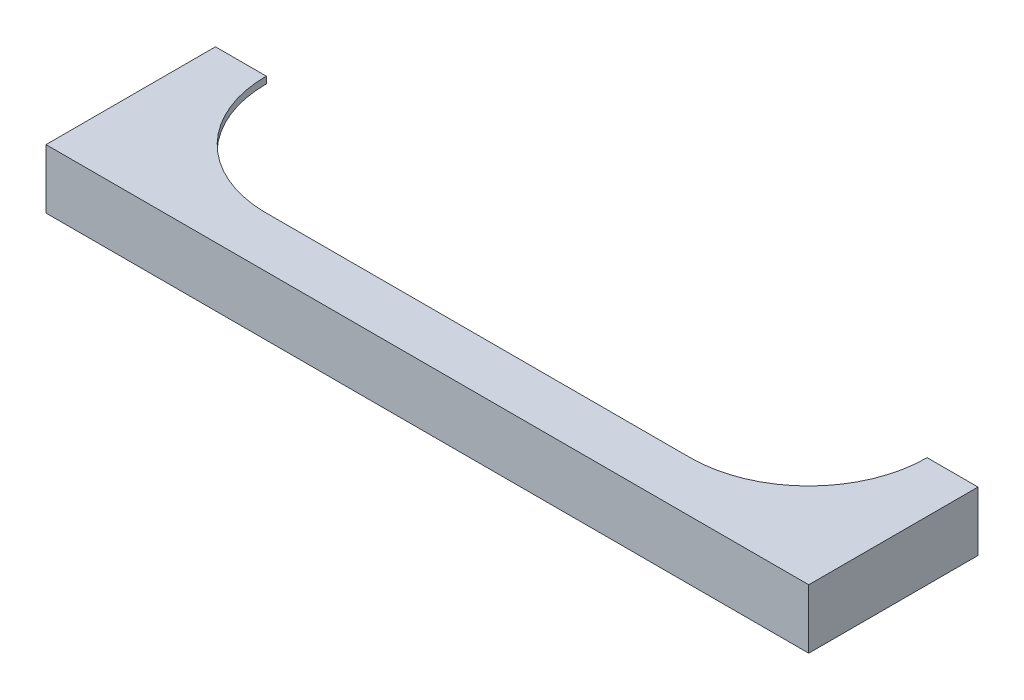
SolidWorks part; units mm, degrees
ref_plane "Front Plane" through (0, 0, 0) normal (0, 0, 1) x (1, 0, 0)
ref_plane "Top Plane" through (0, 0, 0) normal (0, 1, 0) x (1, 0, 0)
ref_plane "Right Plane" through (0, 0, 0) normal (1, 0, 0) x (0, 0, -1)
sketch "Sketch1" plane through (0, 0, 0) normal (0, 1, 0) x (1, 0, 0)
  line L0 (-4500, 0) -> (4499.9997, 2.3515)
  line L1 (-4500, 0) -> (-4500, 2000)
  line L2 (4499.9997, 2.3515) -> (4500, 2000)
  line L3 (4500, 2000) -> (3900, 2000)
  line L4 (-4500, 2000) -> (-3900, 2000)
  line L5 (-2537.8841, 600.5127) -> (2501.8294, 601.8294)
  arc A0 (-3900, 2000) -> (-2537.8841, 600.5127) centre (-2500, 2000) ccw
  arc A1 (3900, 2000) -> (2501.8294, 601.8294) centre (2501.8294, 2000) cw
  point P3 (-0.0002, 1.1757)
  point P8 (0, 0)
  dimension "D1" = 9000
  dimension "D2" = 2000
  dimension "D3" = 600
  dimension "D4" = 600
  dimension "D5" = 600
ref_plane "Plane1" through (0, 0, -2500) normal (0, 0, 1) x (1, 0, 0)
extrude "Boss-Extrude1" add sketch "Sketch1" along normal blind 700
sketch "Sketch6" plane through (0, 0, -2500) normal (0, 0, 1) x (1, 0, 0)
  line L0 (-4460, 0) -> (4460, 0)
  line L1 (4460, 0) -> (4460, 620)
  line L2 (4460, 620) -> (-4460, 620)
  line L3 (-4460, 620) -> (-4460, 0)
  point P3 (0, 0)
  dimension "D1" = 8920
  dimension "D2" = 620
extrude "Cut-Extrude1" cut sketch "Sketch6" along normal blind 2400
